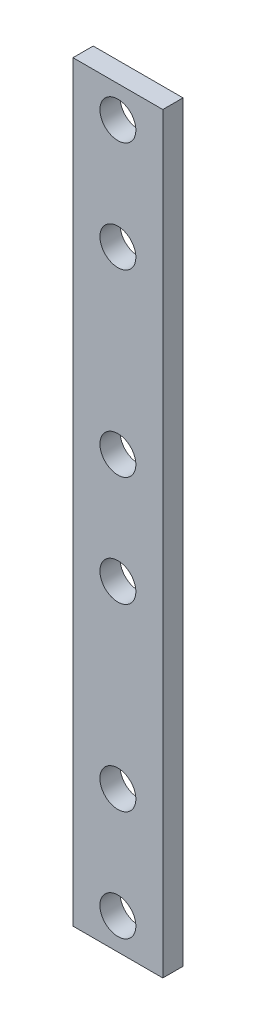
SolidWorks part; units mm, degrees
ref_plane "Front Plane" through (0, 0, 0) normal (0, 0, 1) x (1, 0, 0)
ref_plane "Top Plane" through (0, 0, 0) normal (0, 1, 0) x (1, 0, 0)
ref_plane "Right Plane" through (0, 0, 0) normal (1, 0, 0) x (0, 0, -1)
sketch "Sketch1" plane through (0, 0, 0) normal (0, 0, 1) x (1, 0, 0)
  line L6 (36.342, -82.5) -> (16.342, -82.5)
  line L7 (36.342, -82.5) -> (36.342, 85)
  line L8 (36.342, 85) -> (16.342, 85)
  line L9 (16.342, -82.5) -> (16.342, 85)
extrude "Boss-Extrude1" add sketch "Sketch1" along normal blind 4.5
sketch "Sketch2" plane through (0, 0, 4.5) normal (0, 0, 1) x (1, 0, 0)
  circle A0 centre (26.342, -75.5) radius 4
  circle A1 centre (26.342, -51) radius 4
  circle A2 centre (26.342, -11) radius 4
  circle A3 centre (26.342, 13.5) radius 4
  circle A4 centre (26.342, 53.5) radius 4
  circle A5 centre (26.342, 78) radius 4
  circle A6 centre (26.342, -75.5) radius 4 construction
  circle A7 centre (26.342, -51) radius 4 construction
  circle A8 centre (26.342, -11) radius 4 construction
  circle A9 centre (26.342, 13.5) radius 4 construction
  circle A10 centre (26.342, 53.5) radius 4 construction
  circle A11 centre (26.342, 78) radius 4 construction
extrude "Cut-Extrude1" cut sketch "Sketch2" against normal blind 4.5 contours A0 | A1 | A2 | A3 | A4 | A5
